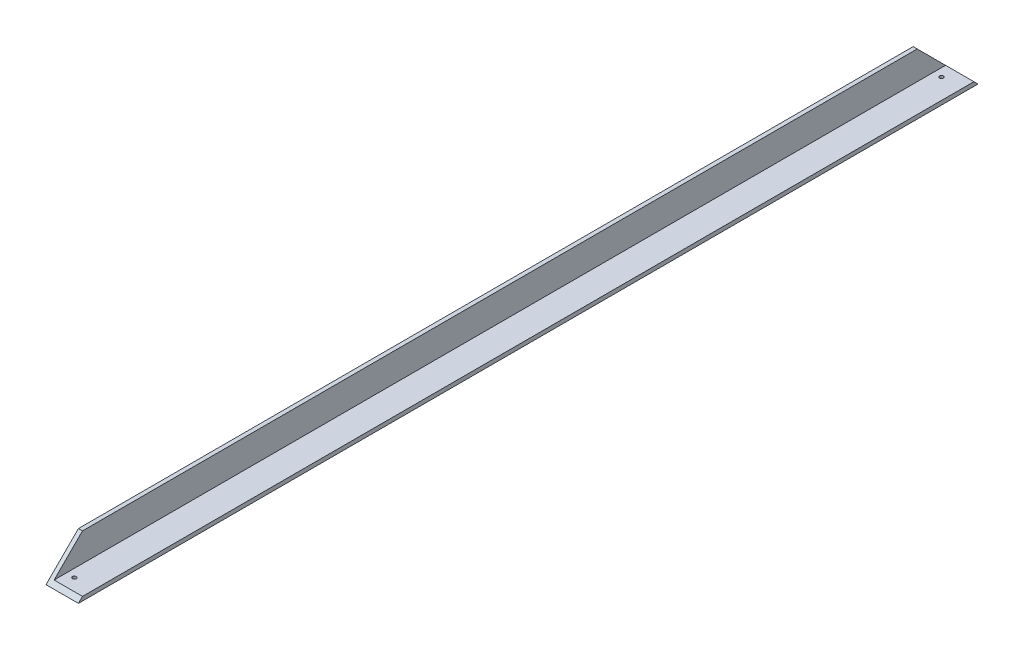
SolidWorks part; units mm, degrees
material "1060-O (SS)"
ref_plane "Front Plane" through (0, 0, 0) normal (0, 0, 1) x (1, 0, 0)
ref_plane "Top Plane" through (0, 0, 0) normal (0, 1, 0) x (1, 0, 0)
ref_plane "Right Plane" through (0, 0, 0) normal (1, 0, 0) x (0, 0, -1)
sketch "Sketch1" plane through (0, 0, 0) normal (0, 0, 1) x (1, 0, 0)
  line L0 (0, 0) -> (0, 34.0895) construction
  line L1 (0, 0) -> (36.0947, 0) construction
  line L2 (0, 25.4) -> (0, 0)
  line L3 (0, 0) -> (25.4, 0)
  line L4 (25.4, 0) -> (25.4, 3.175)
  line L5 (25.4, 3.175) -> (3.175, 3.175)
  line L6 (3.175, 3.175) -> (3.175, 25.4)
  line L7 (3.175, 25.4) -> (0, 25.4)
  dimension "D1" = 25.4
  dimension "D2" = 25.4
  dimension "D3" = 3.175
  dimension "D4" = 3.175
extrude "Boss-Extrude1" add sketch "Sketch1" along normal blind 704.85
sketch "Sketch2" plane through (0, 0, 0) normal (-1, 0, 0) x (0, 0, 1)
  line L0 (0, 0) -> (25.4, 25.4)
  line L1 (704.85, 25.4) -> (0, 25.4) construction
  line L2 (704.85, 0) -> (679.45, 25.4)
  line L3 (0, 0) -> (0, 8.5421)
  line L4 (0, 25.4) -> (0, 0) construction
  line L5 (0, 25.4) -> (25.4, 25.4)
  line L6 (679.45, 25.4) -> (704.85, 25.4)
  line L7 (704.85, 25.4) -> (704.85, 0)
  line M3 (0, 25.4) -> (0, 0)
  line M5 (704.85, 0) -> (704.85, 25.4)
  line M6 (704.85, 25.4) -> (0, 25.4)
  dimension "D1" = 25.4
  dimension "D2" = 25.4
extrude "Cut-Extrude1" cut sketch "Sketch2" against normal blind 711.2 contours L0 M3 M6 | L2 M5 M6
sketch "Sketch3" plane through (0, 0, 0) normal (0, -1, 0) x (1, 0, 0)
  line L0 (0, 0) -> (25.4, 0) construction
  line L1 (0, 704.85) -> (25.4, 704.85) construction
  line L2 (0, 704.85) -> (0, 0) construction
  circle A0 centre (9.525, 692.15) radius 1.5
  circle A1 centre (9.525, 12.7) radius 1.5
  dimension "D1" = 3
  dimension "D2" = 3
  dimension "D3" = 12.7
  dimension "D4" = 12.7
  dimension "D5" = 9.525
  dimension "D6" = 9.525
extrude "Cut-Extrude2" cut sketch "Sketch3" against normal blind 711.2
